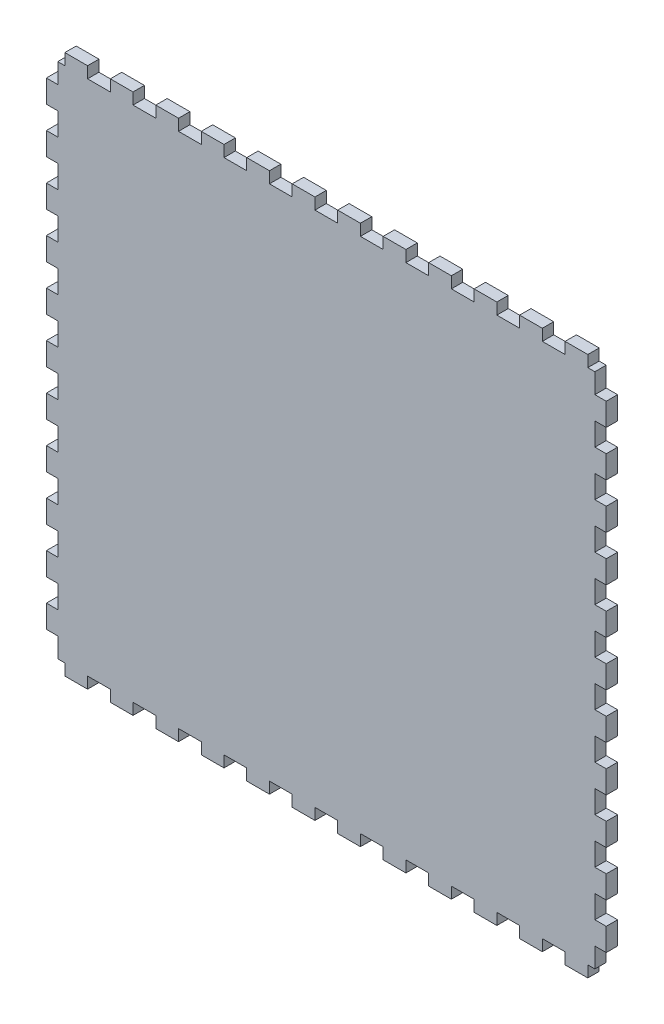
SolidWorks part; units mm, degrees
ref_plane "Front Plane" through (0, 0, 0) normal (0, 0, 1) x (1, 0, 0)
ref_plane "Top Plane" through (0, 0, 0) normal (0, 1, 0) x (1, 0, 0)
ref_plane "Right Plane" through (0, 0, 0) normal (1, 0, 0) x (0, 0, -1)
sketch "Model" plane through (0, 0, 0) normal (0, 0, 1) x (1, 0, 0)
  line L370 (584.6889, 28.5752) -> (588.2463, 28.5752)
  line L371 (588.2463, 28.5752) -> (588.2463, 22.8602)
  line L372 (588.2463, 22.8602) -> (599.6735, 22.8602)
  line L373 (599.6735, 22.8602) -> (599.6735, 28.5752)
  line L374 (599.6735, 28.5752) -> (611.1042, 28.5752)
  line L375 (611.1042, 28.5752) -> (611.1042, 22.8602)
  line L376 (611.1042, 22.8602) -> (622.535, 22.8602)
  line L377 (622.535, 22.8602) -> (622.535, 28.5752)
  line L378 (622.535, 28.5752) -> (633.9657, 28.5752)
  line L379 (633.9657, 28.5752) -> (633.9657, 22.8602)
  line L380 (633.9657, 22.8602) -> (645.3964, 22.8602)
  line L381 (645.3964, 22.8602) -> (645.3964, 28.5752)
  line L382 (645.3964, 28.5752) -> (656.8236, 28.5752)
  line L383 (656.8236, 28.5752) -> (656.8236, 22.8602)
  line L384 (656.8236, 22.8602) -> (668.2543, 22.8602)
  line L385 (668.2543, 22.8602) -> (668.2543, 28.5752)
  line L386 (668.2543, 28.5752) -> (679.685, 28.5752)
  line L387 (679.685, 28.5752) -> (679.685, 22.8602)
  line L388 (679.685, 22.8602) -> (691.1157, 22.8602)
  line L389 (691.1157, 22.8602) -> (691.1157, 28.5752)
  line L390 (691.1157, 28.5752) -> (702.5465, 28.5752)
  line L391 (702.5465, 28.5752) -> (702.5465, 22.8602)
  line L392 (702.5465, 22.8602) -> (713.9736, 22.8602)
  line L393 (713.9736, 22.8602) -> (713.9736, 28.5752)
  line L394 (713.9736, 28.5752) -> (725.4044, 28.5752)
  line L395 (725.4044, 28.5752) -> (725.4044, 22.8602)
  line L396 (725.4044, 22.8602) -> (736.8351, 22.8602)
  line L397 (736.8351, 22.8602) -> (736.8351, 28.5752)
  line L398 (736.8351, 28.5752) -> (748.2658, 28.5752)
  line L399 (748.2658, 28.5752) -> (748.2658, 22.8602)
  line L400 (748.2658, 22.8602) -> (759.6965, 22.8602)
  line L401 (759.6965, 22.8602) -> (759.6965, 28.5752)
  line L402 (759.6965, 28.5752) -> (771.1237, 28.5752)
  line L403 (771.1237, 28.5752) -> (771.1237, 22.8602)
  line L404 (771.1237, 22.8602) -> (782.5544, 22.8602)
  line L405 (782.5544, 22.8602) -> (782.5544, 28.5752)
  line L406 (782.5544, 28.5752) -> (793.9852, 28.5752)
  line L407 (793.9852, 28.5752) -> (793.9852, 22.8602)
  line L408 (793.9852, 22.8602) -> (805.4159, 22.8602)
  line L409 (805.4159, 22.8602) -> (805.4159, 28.5752)
  line L410 (805.4159, 28.5752) -> (816.8466, 28.5752)
  line L411 (816.8466, 28.5752) -> (816.8466, 22.8602)
  line L412 (816.8466, 22.8602) -> (828.2738, 22.8602)
  line L413 (828.2738, 22.8602) -> (828.2738, 28.5752)
  line L414 (828.2738, 28.5752) -> (839.7045, 28.5752)
  line L415 (839.7045, 28.5752) -> (839.7045, 22.8602)
  line L416 (839.7045, 22.8602) -> (851.1352, 22.8602)
  line L417 (851.1352, 22.8602) -> (851.1352, 28.5752)
  line L418 (851.1352, 28.5752) -> (854.6892, 28.5752)
  line L419 (854.6892, 28.5752) -> (854.6892, 38.5601)
  line L420 (854.6892, 38.5601) -> (860.4045, 38.5601)
  line L421 (860.4045, 38.5601) -> (860.4045, 49.9901)
  line L422 (860.4045, 49.9901) -> (854.6892, 49.9901)
  line L423 (854.6892, 49.9901) -> (854.6892, 61.4201)
  line L424 (854.6892, 61.4201) -> (860.4045, 61.4201)
  line L425 (860.4045, 61.4201) -> (860.4045, 72.8501)
  line L426 (860.4045, 72.8501) -> (854.6892, 72.8501)
  line L427 (854.6892, 72.8501) -> (854.6892, 84.2801)
  line L428 (854.6892, 84.2801) -> (860.4045, 84.2801)
  line L429 (860.4045, 84.2801) -> (860.4045, 95.7101)
  line L430 (860.4045, 95.7101) -> (854.6892, 95.7101)
  line L431 (854.6892, 95.7101) -> (854.6892, 107.1402)
  line L432 (854.6892, 107.1402) -> (860.4045, 107.1402)
  line L433 (860.4045, 107.1402) -> (860.4045, 118.5702)
  line L434 (860.4045, 118.5702) -> (854.6892, 118.5702)
  line L435 (854.6892, 118.5702) -> (854.6892, 130.0002)
  line L436 (854.6892, 130.0002) -> (860.4045, 130.0002)
  line L437 (860.4045, 130.0002) -> (860.4045, 141.4302)
  line L438 (860.4045, 141.4302) -> (854.6892, 141.4302)
  line L439 (854.6892, 141.4302) -> (854.6892, 152.8602)
  line L440 (854.6892, 152.8602) -> (860.4045, 152.8602)
  line L441 (860.4045, 152.8602) -> (860.4045, 164.2902)
  line L442 (860.4045, 164.2902) -> (854.6892, 164.2902)
  line L443 (854.6892, 164.2902) -> (854.6892, 175.7202)
  line L444 (854.6892, 175.7202) -> (860.4045, 175.7202)
  line L445 (860.4045, 175.7202) -> (860.4045, 187.1503)
  line L446 (860.4045, 187.1503) -> (854.6892, 187.1503)
  line L447 (854.6892, 187.1503) -> (854.6892, 198.5803)
  line L448 (854.6892, 198.5803) -> (860.4045, 198.5803)
  line L449 (860.4045, 198.5803) -> (860.4045, 210.0103)
  line L450 (860.4045, 210.0103) -> (854.6892, 210.0103)
  line L451 (854.6892, 210.0103) -> (854.6892, 221.4403)
  line L452 (854.6892, 221.4403) -> (860.4045, 221.4403)
  line L453 (860.4045, 221.4403) -> (860.4045, 232.8703)
  line L454 (860.4045, 232.8703) -> (854.6892, 232.8703)
  line L455 (854.6892, 232.8703) -> (854.6892, 244.3003)
  line L456 (854.6892, 244.3003) -> (860.4045, 244.3003)
  line L457 (860.4045, 244.3003) -> (860.4045, 255.7303)
  line L458 (860.4045, 255.7303) -> (854.6892, 255.7303)
  line L459 (854.6892, 255.7303) -> (854.6892, 267.1603)
  line L460 (854.6892, 267.1603) -> (860.4045, 267.1603)
  line L461 (860.4045, 267.1603) -> (860.4045, 278.5904)
  line L462 (860.4045, 278.5904) -> (854.6892, 278.5904)
  line L463 (854.6892, 278.5904) -> (854.6892, 288.5754)
  line L464 (854.6892, 288.5754) -> (851.1352, 288.5754)
  line L465 (851.1352, 288.5754) -> (851.1352, 294.2904)
  line L466 (851.1352, 294.2904) -> (839.7045, 294.2904)
  line L467 (839.7045, 294.2904) -> (839.7045, 288.5754)
  line L468 (839.7045, 288.5754) -> (828.2738, 288.5754)
  line L469 (828.2738, 288.5754) -> (828.2738, 294.2904)
  line L470 (828.2738, 294.2904) -> (816.8466, 294.2904)
  line L471 (816.8466, 294.2904) -> (816.8466, 288.5754)
  line L472 (816.8466, 288.5754) -> (805.4159, 288.5754)
  line L473 (805.4159, 288.5754) -> (805.4159, 294.2904)
  line L474 (805.4159, 294.2904) -> (793.9852, 294.2904)
  line L475 (793.9852, 294.2904) -> (793.9852, 288.5754)
  line L476 (793.9852, 288.5754) -> (782.5544, 288.5754)
  line L477 (782.5544, 288.5754) -> (782.5544, 294.2904)
  line L478 (782.5544, 294.2904) -> (771.1237, 294.2904)
  line L479 (771.1237, 294.2904) -> (771.1237, 288.5754)
  line L480 (771.1237, 288.5754) -> (759.6965, 288.5754)
  line L481 (759.6965, 288.5754) -> (759.6965, 294.2904)
  line L482 (759.6965, 294.2904) -> (748.2658, 294.2904)
  line L483 (748.2658, 294.2904) -> (748.2658, 288.5754)
  line L484 (748.2658, 288.5754) -> (736.8351, 288.5754)
  line L485 (736.8351, 288.5754) -> (736.8351, 294.2904)
  line L486 (736.8351, 294.2904) -> (725.4044, 294.2904)
  line L487 (725.4044, 294.2904) -> (725.4044, 288.5754)
  line L488 (725.4044, 288.5754) -> (713.9736, 288.5754)
  line L489 (713.9736, 288.5754) -> (713.9736, 294.2904)
  line L490 (713.9736, 294.2904) -> (702.5465, 294.2904)
  line L491 (702.5465, 294.2904) -> (702.5465, 288.5754)
  line L492 (702.5465, 288.5754) -> (691.1157, 288.5754)
  line L493 (691.1157, 288.5754) -> (691.1157, 294.2904)
  line L494 (691.1157, 294.2904) -> (679.685, 294.2904)
  line L495 (679.685, 294.2904) -> (679.685, 288.5754)
  line L496 (679.685, 288.5754) -> (668.2543, 288.5754)
  line L497 (668.2543, 288.5754) -> (668.2543, 294.2904)
  line L498 (668.2543, 294.2904) -> (656.8236, 294.2904)
  line L499 (656.8236, 294.2904) -> (656.8236, 288.5754)
  line L500 (656.8236, 288.5754) -> (645.3964, 288.5754)
  line L501 (645.3964, 288.5754) -> (645.3964, 294.2904)
  line L502 (645.3964, 294.2904) -> (633.9657, 294.2904)
  line L503 (633.9657, 294.2904) -> (633.9657, 288.5754)
  line L504 (633.9657, 288.5754) -> (622.535, 288.5754)
  line L505 (622.535, 288.5754) -> (622.535, 294.2904)
  line L506 (622.535, 294.2904) -> (611.1042, 294.2904)
  line L507 (611.1042, 294.2904) -> (611.1042, 288.5754)
  line L508 (611.1042, 288.5754) -> (599.6735, 288.5754)
  line L509 (599.6735, 288.5754) -> (599.6735, 294.2904)
  line L510 (599.6735, 294.2904) -> (588.2463, 294.2904)
  line L511 (588.2463, 294.2904) -> (588.2463, 288.5754)
  line L512 (588.2463, 288.5754) -> (584.6889, 288.5754)
  line L513 (584.6889, 288.5754) -> (584.6889, 278.5904)
  line L514 (584.6889, 278.5904) -> (578.9735, 278.5904)
  line L515 (578.9735, 278.5904) -> (578.9735, 267.1603)
  line L516 (578.9735, 267.1603) -> (584.6889, 267.1603)
  line L517 (584.6889, 267.1603) -> (584.6889, 255.7303)
  line L518 (584.6889, 255.7303) -> (578.9735, 255.7303)
  line L519 (578.9735, 255.7303) -> (578.9735, 244.3003)
  line L520 (578.9735, 244.3003) -> (584.6889, 244.3003)
  line L521 (584.6889, 244.3003) -> (584.6889, 232.8703)
  line L522 (584.6889, 232.8703) -> (578.9735, 232.8703)
  line L523 (578.9735, 232.8703) -> (578.9735, 221.4403)
  line L524 (578.9735, 221.4403) -> (584.6889, 221.4403)
  line L525 (584.6889, 221.4403) -> (584.6889, 210.0103)
  line L526 (584.6889, 210.0103) -> (578.9735, 210.0103)
  line L527 (578.9735, 210.0103) -> (578.9735, 198.5803)
  line L528 (578.9735, 198.5803) -> (584.6889, 198.5803)
  line L529 (584.6889, 198.5803) -> (584.6889, 187.1503)
  line L530 (584.6889, 187.1503) -> (578.9735, 187.1503)
  line L531 (578.9735, 187.1503) -> (578.9735, 175.7202)
  line L532 (578.9735, 175.7202) -> (584.6889, 175.7202)
  line L533 (584.6889, 175.7202) -> (584.6889, 164.2902)
  line L534 (584.6889, 164.2902) -> (578.9735, 164.2902)
  line L535 (578.9735, 164.2902) -> (578.9735, 152.8602)
  line L536 (578.9735, 152.8602) -> (584.6889, 152.8602)
  line L537 (584.6889, 152.8602) -> (584.6889, 141.4302)
  line L538 (584.6889, 141.4302) -> (578.9735, 141.4302)
  line L539 (578.9735, 141.4302) -> (578.9735, 130.0002)
  line L540 (578.9735, 130.0002) -> (584.6889, 130.0002)
  line L541 (584.6889, 130.0002) -> (584.6889, 118.5702)
  line L542 (584.6889, 118.5702) -> (578.9735, 118.5702)
  line L543 (578.9735, 118.5702) -> (578.9735, 107.1402)
  line L544 (578.9735, 107.1402) -> (584.6889, 107.1402)
  line L545 (584.6889, 107.1402) -> (584.6889, 95.7101)
  line L546 (584.6889, 95.7101) -> (578.9735, 95.7101)
  line L547 (578.9735, 95.7101) -> (578.9735, 84.2801)
  line L548 (578.9735, 84.2801) -> (584.6889, 84.2801)
  line L549 (584.6889, 84.2801) -> (584.6889, 72.8501)
  line L550 (584.6889, 72.8501) -> (578.9735, 72.8501)
  line L551 (578.9735, 72.8501) -> (578.9735, 61.4201)
  line L552 (578.9735, 61.4201) -> (584.6889, 61.4201)
  line L553 (584.6889, 61.4201) -> (584.6889, 49.9901)
  line L554 (584.6889, 49.9901) -> (578.9735, 49.9901)
  line L555 (578.9735, 49.9901) -> (578.9735, 38.5601)
  line L556 (578.9735, 38.5601) -> (584.6889, 38.5601)
  line L557 (584.6889, 38.5601) -> (584.6889, 28.5752)
extrude "Boss-Extrude1" add sketch "Model" along normal blind 5.715
